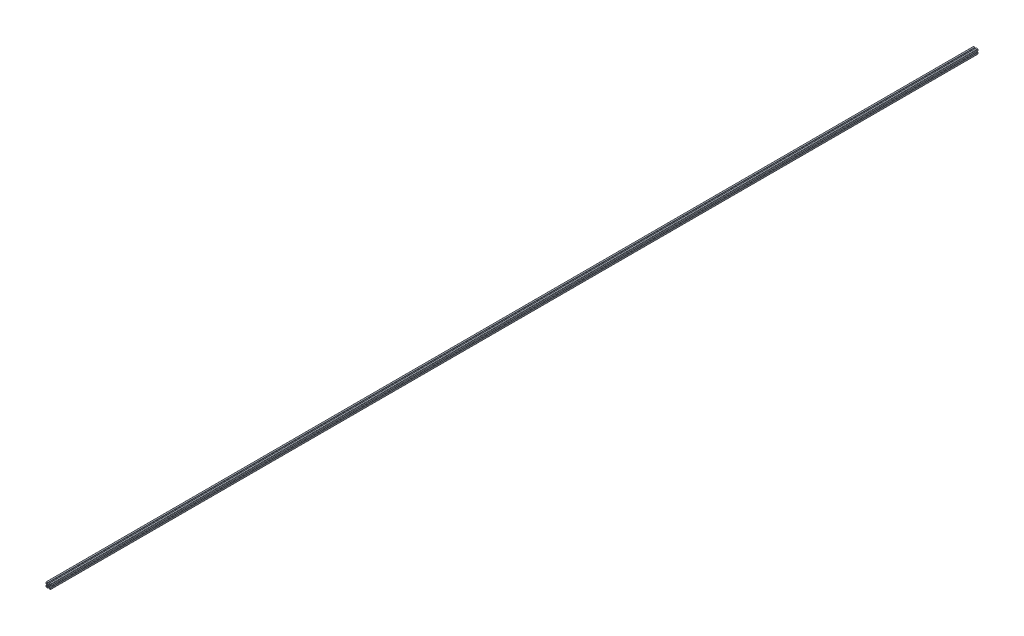
SolidWorks part; units mm, degrees
ref_plane "Front Plane" through (0, 0, 0) normal (0, 0, 1) x (1, 0, 0)
ref_plane "Top Plane" through (0, 0, 0) normal (0, 1, 0) x (1, 0, 0)
ref_plane "Right Plane" through (0, 0, 0) normal (1, 0, 0) x (0, 0, -1)
sketch "Sketch1" plane through (0, 0, 0) normal (0, 0, 1) x (1, 0, 0)
  line L0 (-5.0323, -0.3411) -> (-5.5163, -0.3411)
  line L1 (-6.0243, 0.1669) -> (-6.0243, 2.5159)
  line L2 (-4.5243, 0.1669) -> (-4.5243, 5.5289)
  line L3 (-10.8693, -5.355) -> (-10.8693, -0.5871)
  line L4 (-7.2582, 3.0239) -> (-6.5323, 3.0239)
  line L5 (-7.6174, 2.8752) -> (-10.7205, -0.2279)
  line L6 (-5.0323, -5.6011) -> (-5.5163, -5.6011)
  line L7 (-4.5243, -6.1091) -> (-4.5243, -11.4711)
  line L8 (-6.0243, -6.1091) -> (-6.0243, -8.4581)
  line L9 (-7.2582, -8.9661) -> (-6.5323, -8.9661)
  line L10 (-7.6174, -8.8173) -> (-10.7205, -5.7142)
  line L11 (-12.3994, -5.2756) -> (-12.2198, -5.096)
  line L12 (-17.1543, 6.5209) -> (-17.1543, 6.0369)
  line L13 (-17.6623, 7.0289) -> (-23.0243, 7.0289)
  line L14 (-17.6623, 5.5289) -> (-20.0113, 5.5289)
  line L15 (-12.1404, 0.6839) -> (-16.9082, 0.6839)
  line L16 (-20.5193, 4.295) -> (-20.5193, 5.0209)
  line L17 (-20.3705, 3.9358) -> (-17.2674, 0.8327)
  line L18 (-11.8943, 6.5209) -> (-11.8943, 6.0369)
  line L19 (-11.3863, 7.0289) -> (-6.0243, 7.0289)
  line L20 (-11.3863, 5.5289) -> (-9.0373, 5.5289)
  line L21 (-8.5293, 4.295) -> (-8.5293, 5.0209)
  line L22 (-8.6781, 3.9358) -> (-11.7812, 0.8327)
  line L23 (-12.2198, -0.8462) -> (-12.3994, -0.6666)
  line L24 (-24.0163, -5.6011) -> (-23.5323, -5.6011)
  line L25 (-24.5243, -6.1091) -> (-24.5243, -11.4711)
  line L26 (-23.0243, -6.1091) -> (-23.0243, -8.4581)
  line L27 (-18.1793, -0.5871) -> (-18.1793, -5.355)
  line L28 (-21.7904, -8.9661) -> (-22.5163, -8.9661)
  line L29 (-21.4312, -8.8173) -> (-18.3281, -5.7142)
  line L30 (-24.0163, -0.3411) -> (-23.5323, -0.3411)
  line L31 (-24.5243, 0.1669) -> (-24.5243, 5.5289)
  line L32 (-23.0243, 0.1669) -> (-23.0243, 2.5159)
  line L33 (-21.7904, 3.0239) -> (-22.5163, 3.0239)
  line L34 (-21.4312, 2.8752) -> (-18.3281, -0.2279)
  line L35 (-16.6492, -0.6666) -> (-16.8288, -0.8462)
  line L36 (-11.8943, -12.4631) -> (-11.8943, -11.9791)
  line L37 (-11.3863, -12.9711) -> (-6.0243, -12.9711)
  line L38 (-11.3863, -11.4711) -> (-9.0373, -11.4711)
  line L39 (-16.9082, -6.6261) -> (-12.1404, -6.6261)
  line L40 (-8.5293, -10.2371) -> (-8.5293, -10.9631)
  line L41 (-8.6781, -9.8779) -> (-11.7812, -6.7748)
  line L42 (-17.1543, -12.4631) -> (-17.1543, -11.9791)
  line L43 (-17.6623, -12.9711) -> (-23.0243, -12.9711)
  line L44 (-17.6623, -11.4711) -> (-20.0113, -11.4711)
  line L45 (-20.5193, -10.2371) -> (-20.5193, -10.9631)
  line L46 (-20.3705, -9.8779) -> (-17.2674, -6.7748)
  line L47 (-16.8288, -5.096) -> (-16.6492, -5.2756)
  arc A0 (-15.3283, -4.9062) -> (-13.7203, -4.9062) centre (-14.5243, -2.9711) ccw
  arc A1 (-6.0243, 2.5159) -> (-6.5323, 3.0239) centre (-6.5323, 2.5159) ccw
  arc A2 (-7.2582, 3.0239) -> (-7.6174, 2.8752) centre (-7.2582, 2.5159) ccw
  arc A3 (-10.7205, -0.2279) -> (-10.8693, -0.5871) centre (-10.3613, -0.5871) ccw
  arc A4 (-10.8693, -5.355) -> (-10.7205, -5.7142) centre (-10.3613, -5.355) ccw
  arc A5 (-7.6174, -8.8173) -> (-7.2582, -8.9661) centre (-7.2582, -8.4581) ccw
  arc A6 (-6.5323, -8.9661) -> (-6.0243, -8.4581) centre (-6.5323, -8.4581) ccw
  arc A7 (-5.5163, -5.6011) -> (-6.0243, -6.1091) centre (-5.5163, -6.1091) ccw
  arc A8 (-4.5243, -6.1091) -> (-5.0323, -5.6011) centre (-5.0323, -6.1091) ccw
  arc A9 (-5.0323, -0.3411) -> (-4.5243, 0.1669) centre (-5.0323, 0.1669) ccw
  arc A10 (-6.0243, 0.1669) -> (-5.5163, -0.3411) centre (-5.5163, 0.1669) ccw
  arc A11 (-13.7203, -4.9062) -> (-12.3994, -5.2756) centre (-12.9559, -4.7191) ccw
  arc A12 (-12.2198, -5.096) -> (-12.5892, -3.775) centre (-12.7763, -4.5395) ccw
  arc A13 (-17.1543, 6.5209) -> (-17.6623, 7.0289) centre (-17.6623, 6.5209) ccw
  arc A14 (-17.6623, 5.5289) -> (-17.1543, 6.0369) centre (-17.6623, 6.0369) ccw
  arc A15 (-12.5892, -3.775) -> (-12.5892, -2.1671) centre (-14.5243, -2.9711) ccw
  arc A16 (-17.2674, 0.8327) -> (-16.9082, 0.6839) centre (-16.9082, 1.1919) ccw
  arc A17 (-20.0113, 5.5289) -> (-20.5193, 5.0209) centre (-20.0113, 5.0209) ccw
  arc A18 (-20.5193, 4.295) -> (-20.3705, 3.9358) centre (-20.0113, 4.295) ccw
  arc A19 (-11.8943, 6.0369) -> (-11.3863, 5.5289) centre (-11.3863, 6.0369) ccw
  arc A20 (-11.3863, 7.0289) -> (-11.8943, 6.5209) centre (-11.3863, 6.5209) ccw
  arc A21 (-8.5293, 5.0209) -> (-9.0373, 5.5289) centre (-9.0373, 5.0209) ccw
  arc A22 (-8.6781, 3.9358) -> (-8.5293, 4.295) centre (-9.0373, 4.295) ccw
  arc A23 (-12.1404, 0.6839) -> (-11.7812, 0.8327) centre (-12.1404, 1.1919) ccw
  arc A24 (-12.5892, -2.1671) -> (-12.2198, -0.8462) centre (-12.7763, -1.4027) ccw
  arc A25 (-12.3994, -0.6666) -> (-13.7203, -1.0359) centre (-12.9559, -1.223) ccw
  arc A26 (-24.0163, -5.6011) -> (-24.5243, -6.1091) centre (-24.0163, -6.1091) ccw
  arc A27 (-23.0243, -6.1091) -> (-23.5323, -5.6011) centre (-23.5323, -6.1091) ccw
  arc A28 (-13.7203, -1.0359) -> (-15.3283, -1.0359) centre (-14.5243, -2.9711) ccw
  arc A29 (-18.3281, -5.7142) -> (-18.1793, -5.355) centre (-18.6873, -5.355) ccw
  arc A30 (-23.0243, -8.4581) -> (-22.5163, -8.9661) centre (-22.5163, -8.4581) ccw
  arc A31 (-21.7904, -8.9661) -> (-21.4312, -8.8173) centre (-21.7904, -8.4581) ccw
  arc A32 (-23.5323, -0.3411) -> (-23.0243, 0.1669) centre (-23.5323, 0.1669) ccw
  arc A33 (-24.5243, 0.1669) -> (-24.0163, -0.3411) centre (-24.0163, 0.1669) ccw
  arc A34 (-22.5163, 3.0239) -> (-23.0243, 2.5159) centre (-22.5163, 2.5159) ccw
  arc A35 (-21.4312, 2.8752) -> (-21.7904, 3.0239) centre (-21.7904, 2.5159) ccw
  arc A36 (-18.1793, -0.5871) -> (-18.3281, -0.2279) centre (-18.6873, -0.5871) ccw
  arc A37 (-15.3283, -1.0359) -> (-16.6492, -0.6666) centre (-16.0927, -1.223) ccw
  arc A38 (-16.8288, -0.8462) -> (-16.4594, -2.1671) centre (-16.2723, -1.4027) ccw
  arc A39 (-11.8943, -12.4631) -> (-11.3863, -12.9711) centre (-11.3863, -12.4631) ccw
  arc A40 (-11.3863, -11.4711) -> (-11.8943, -11.9791) centre (-11.3863, -11.9791) ccw
  arc A41 (-16.4594, -2.1671) -> (-16.4594, -3.775) centre (-14.5243, -2.9711) ccw
  arc A42 (-11.7812, -6.7748) -> (-12.1404, -6.6261) centre (-12.1404, -7.1341) ccw
  arc A43 (-9.0373, -11.4711) -> (-8.5293, -10.9631) centre (-9.0373, -10.9631) ccw
  arc A44 (-8.5293, -10.2371) -> (-8.6781, -9.8779) centre (-9.0373, -10.2371) ccw
  arc A45 (-17.1543, -11.9791) -> (-17.6623, -11.4711) centre (-17.6623, -11.9791) ccw
  arc A46 (-17.6623, -12.9711) -> (-17.1543, -12.4631) centre (-17.6623, -12.4631) ccw
  arc A47 (-20.5193, -10.9631) -> (-20.0113, -11.4711) centre (-20.0113, -10.9631) ccw
  arc A48 (-20.3705, -9.8779) -> (-20.5193, -10.2371) centre (-20.0113, -10.2371) ccw
  arc A49 (-16.9082, -6.6261) -> (-17.2674, -6.7748) centre (-16.9082, -7.1341) ccw
  arc A50 (-16.4594, -3.775) -> (-16.8288, -5.096) centre (-16.2723, -4.5395) ccw
  arc A51 (-16.6492, -5.2756) -> (-15.3283, -4.9062) centre (-16.0927, -4.7191) ccw
  arc A52 (-4.5243, 5.5289) -> (-6.0243, 7.0289) centre (-6.0243, 5.5289) ccw
  arc A53 (-6.0243, -12.9711) -> (-4.5243, -11.4711) centre (-6.0243, -11.4711) ccw
  arc A54 (-24.5243, -11.4711) -> (-23.0243, -12.9711) centre (-23.0243, -11.4711) ccw
  arc A55 (-23.0243, 7.0289) -> (-24.5243, 5.5289) centre (-23.0243, 5.5289) ccw
extrude "Extrude1" add sketch "Sketch1" along normal blind 4000
